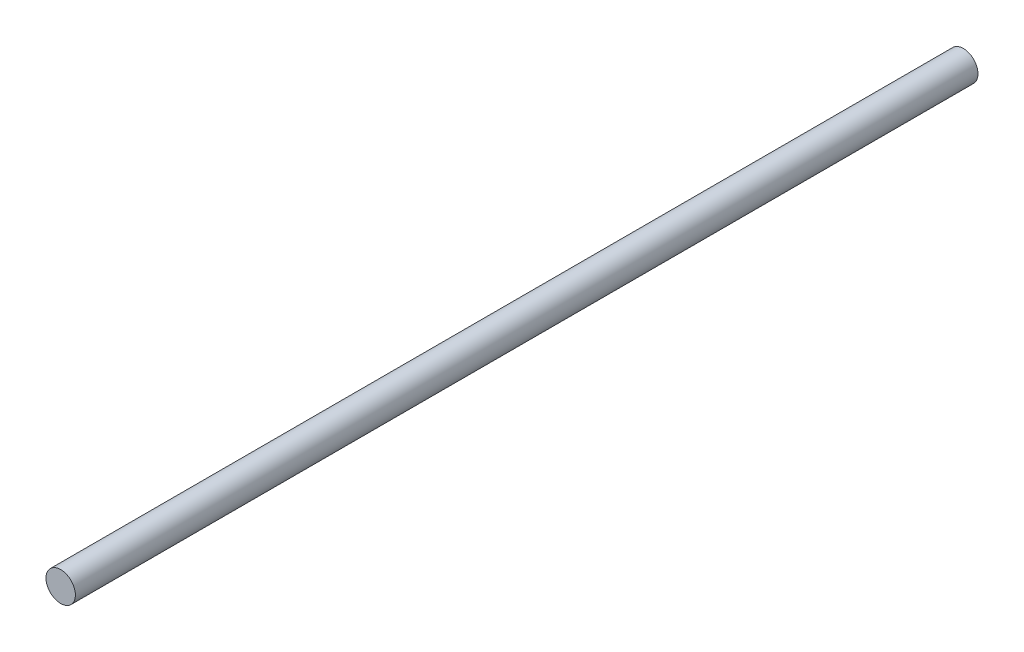
SolidWorks part; units mm, degrees
ref_plane "Front Plane" through (0, 0, 0) normal (0, 0, 1) x (1, 0, 0)
ref_plane "Top Plane" through (0, 0, 0) normal (0, 1, 0) x (1, 0, 0)
ref_plane "Right Plane" through (0, 0, 0) normal (1, 0, 0) x (0, 0, -1)
sketch "Sketch1" plane through (0, 0, 0) normal (0, 0, 1) x (1, 0, 0)
  circle A0 centre (0, 0) radius 2.95
extrude "Boss-Extrude1" add sketch "Sketch1" along normal blind 181
